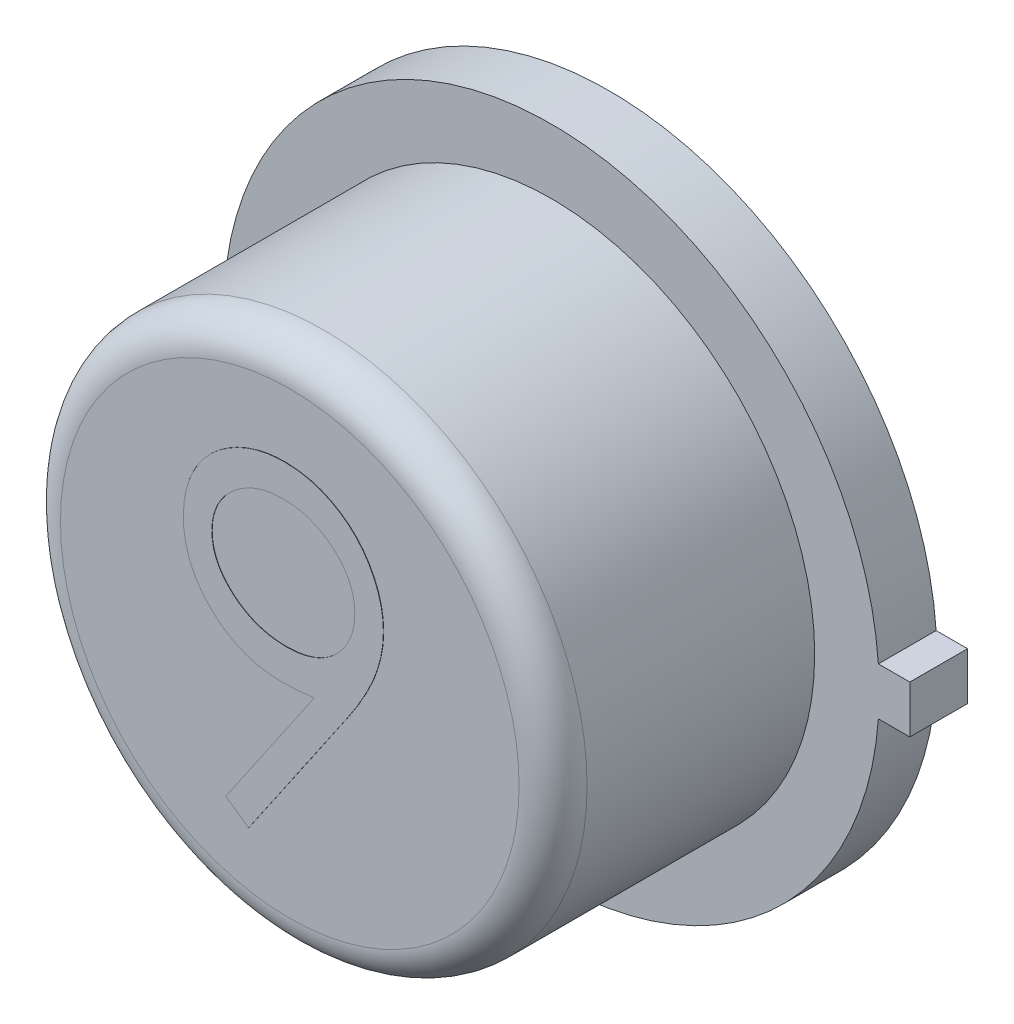
SolidWorks part; units mm, degrees
ref_plane "Front Plane" through (0, 0, 0) normal (0, 0, 1) x (1, 0, 0)
ref_plane "Top Plane" through (0, 0, 0) normal (0, 1, 0) x (1, 0, 0)
ref_plane "Right Plane" through (0, 0, 0) normal (1, 0, 0) x (0, 0, -1)
sketch "Sketch1" plane through (0, 0, 0) normal (0, 0, 1) x (1, 0, 0)
  line L1 (2.4511, 0.1778) -> (2.6797, 0.1778)
  line L3 (2.4511, -0.1778) -> (2.6797, -0.1778)
  line L4 (2.6797, 0.1778) -> (2.6797, -0.1778)
  line L5 (2.4511, 0.1778) -> (2.4444, 0.1778)
  line L6 (2.4511, -0.1778) -> (2.4446, -0.1778)
  arc A0 (2.4446, 0.1778) -> (2.4446, -0.1778) centre (0, 0) ccw
  dimension "D1" = 4.9022
  dimension "D2" = 0.3556
  dimension "D3" = 0.2286
extrude "Boss-Extrude1" add sketch "Sketch1" along normal blind 0.4318
sketch "Sketch2" plane through (0, 0, 0.4318) normal (0, 0, 1) x (1, 0, 0)
  circle A0 centre (0, 0) radius 1.9685
  dimension "D1" = 3.937
extrude "Boss-Extrude2" add sketch "Sketch2" along normal blind 1.9558
sketch "Sketch3" plane through (0, 0, 0) normal (0, 0, -1) x (-1, 0, 0)
  circle A0 centre (0, 0) radius 1.7576
extrude "Boss-Extrude3" add sketch "Sketch3" along normal blind 0.0025
fillet "Fillet1" radius 0.254 1 edges at (1.9685, 0, 2.3876)
sketch "Sketch4" plane through (0, 0, 2.3876) normal (0, 0, 1) x (1, 0, 0)
  line L0 (-1.2065, -1.2181) -> (1.2065, -1.2181) construction
  circle A0 centre (0, 0) radius 1.7145 construction
  text T0 "9" font "Century Gothic" height in points 9
  dimension "D1" = 2.413
extrude "Boss-Extrude6" add sketch "Sketch4" along normal blind 0.0025
